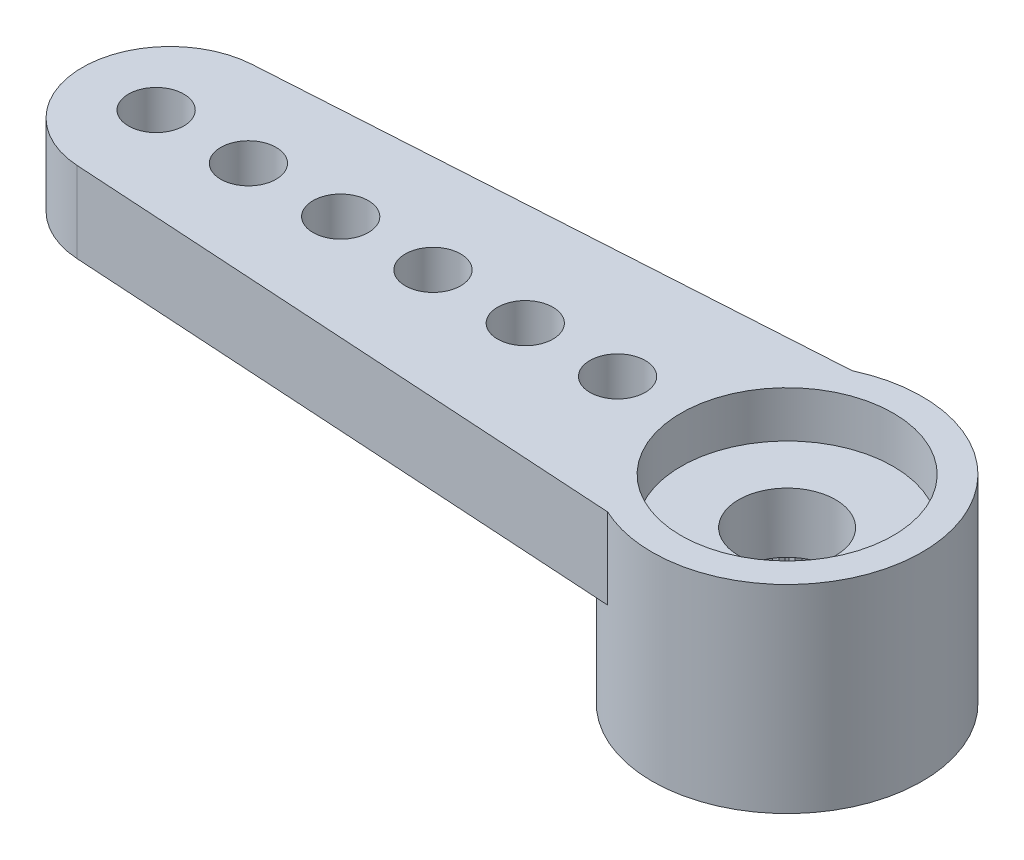
SolidWorks part; units mm, degrees
material "PVC Rígido"
ref_plane "Plano frontal" through (0, 0, 0) normal (0, 0, 1) x (1, 0, 0)
ref_plane "Plano superior" through (0, 0, 0) normal (0, 1, 0) x (1, 0, 0)
ref_plane "Plano direito" through (0, 0, 0) normal (1, 0, 0) x (0, 0, -1)
sketch "Esboço1" plane through (0, 0, 0) normal (0, 1, 0) x (1, 0, 0)
  line L0 (0, 0) -> (-13.375, 0) construction
  line L1 (-13.4916, 1.8964) -> (-1.2382, 2.65)
  line L2 (-1.2382, -2.65) -> (-13.4916, -1.8964)
  arc A0 (-1.2382, -2.65) -> (-1.2382, 2.65) centre (0, 0) ccw
  arc A1 (-13.4916, 1.8964) -> (-13.4916, -1.8964) centre (-13.375, 0) ccw
  dimension "D1" = 5.85
  dimension "D2" = 3.8
  dimension "D3" = 18.2
  dimension "D4" = 5.3
extrude "Ressalto-extrusão1" add sketch "Esboço1" against normal blind 1.75
sketch "Esboço2" plane through (0, -1.75, 0) normal (0, -1, 0) x (1, 0, 0)
  arc A0 (-1.2382, -2.65) -> (-1.2382, 2.65) centre (0, 0) ccw construction
  circle A1 centre (0, 0) radius 2.925
extrude "Ressalto-extrusão2" add sketch "Esboço2" along normal offset from surface (2.55 mm away) 4.3 up to face at (-6.77, 0, 0)
hole_wizard "Furo4" positions "Esboço9" profile "Esboço10" legacy end condition through all
sketch "Esboço9" plane through (0, 0, 0) normal (0, 1, 0) x (1, 0, 0)
  line L1 (-13.675, 0) -> (0, 0) construction
  arc A2 (-13.4916, 1.8964) -> (-13.4916, -1.8964) centre (-13.375, 0) ccw construction
  point P0 (-13.675, 0)
  point P19 (-15.275, 0)
  dimension "D1" = 1.6
sketch "Esboço10" plane through (-13.675, 0, 0) normal (1, 0, 0) x (0, 0, 1)
  line L0 (0, 0) -> (0, 4.3)
  line L1 (0, 4.3) -> (0.6, 4.3)
  line L2 (0.6, 4.3) -> (0.6, 0)
  line L3 (0.6, 0) -> (0, 0)
  line L4 (0, 110) -> (0, -10) construction
  dimension "Diameter" = 1.2
  dimension "Depth" = 4.3
pattern_linear "Padrão linear1" count 6 spacing 2 along (1, 0, 0) of "Furo4"
hole_wizard "Furo1" positions "Esboço3" profile "Esboço4" legacy
sketch "Esboço3" plane through (0, -4.3, 0) normal (0, -1, 0) x (-1, 0, 0)
  point P0 (0, 0)
sketch "Esboço4" plane through (0, -4.3, 0) normal (1, 0, 0) x (0, 0, -1)
  line L0 (0, 0) -> (0, 2)
  line L1 (0, 2) -> (2.475, 2)
  line L2 (2.475, 2) -> (2.475, 0)
  line L3 (2.475, 0) -> (0, 0)
  line L4 (0, 110) -> (0, -10) construction
  dimension "Diameter" = 4.95
  dimension "Depth" = 2
hole_wizard "Furo2" positions "Esboço5" profile "Esboço6" legacy
sketch "Esboço5" plane through (0, 0, 0) normal (0, 1, 0) x (1, 0, 0)
  point P0 (0, 0)
sketch "Esboço6" plane through (0, 0, 0) normal (1, 0, 0) x (0, 0, 1)
  line L0 (0, 0) -> (0, 1)
  line L1 (0, 1) -> (2.3, 1)
  line L2 (2.3, 1) -> (2.3, 0)
  line L3 (2.3, 0) -> (0, 0)
  line L4 (0, 110) -> (0, -10) construction
  dimension "Diameter" = 4.6
  dimension "Depth" = 1
hole_wizard "Furo3" positions "Esboço7" profile "Esboço8" legacy end condition through all
sketch "Esboço7" plane through (0, 0, 0) normal (0, 1, 0) x (1, 0, 0)
  point P0 (0, 0)
sketch "Esboço8" plane through (0, 0, 0) normal (1, 0, 0) x (0, 0, 1)
  line L0 (0, 0) -> (0, 4.3)
  line L1 (0, 4.3) -> (1.05, 4.3)
  line L2 (1.05, 4.3) -> (1.05, 0)
  line L3 (1.05, 0) -> (0, 0)
  line L4 (0, 110) -> (0, -10) construction
  dimension "Diameter" = 2.1
  dimension "Depth" = 4.3
sketch "Esboço11" plane through (0, -4.3, 0) normal (0, -1, 0) x (1, 0, 0)
  line L0 (-0.0981, 2.4731) -> (0, 2.375)
  line L1 (0, 2.375) -> (0.0981, 2.4731)
  line L2 (0, 0) -> (0, 2.475) construction
  circle A0 centre (0, 0) radius 2.375 construction
  circle A1 centre (0, 0) radius 2.475
  arc A2 (0.0981, 2.4731) -> (-0.0981, 2.4731) centre (0, 0) ccw
  dimension "D3" = 4.75
  dimension "D2" = 0.1
  dimension "D1" = 0
extrude "Ressalto-extrusão3" add sketch "Esboço11" against normal up to surface (2 mm away) up to face at (0, -2.3, 1.05)
pattern_circular "PadrãoCircular1" count 60 over 360 about axis through (0, 0, 0) along (0, 1, 0) of "Ressalto-extrusão3"
